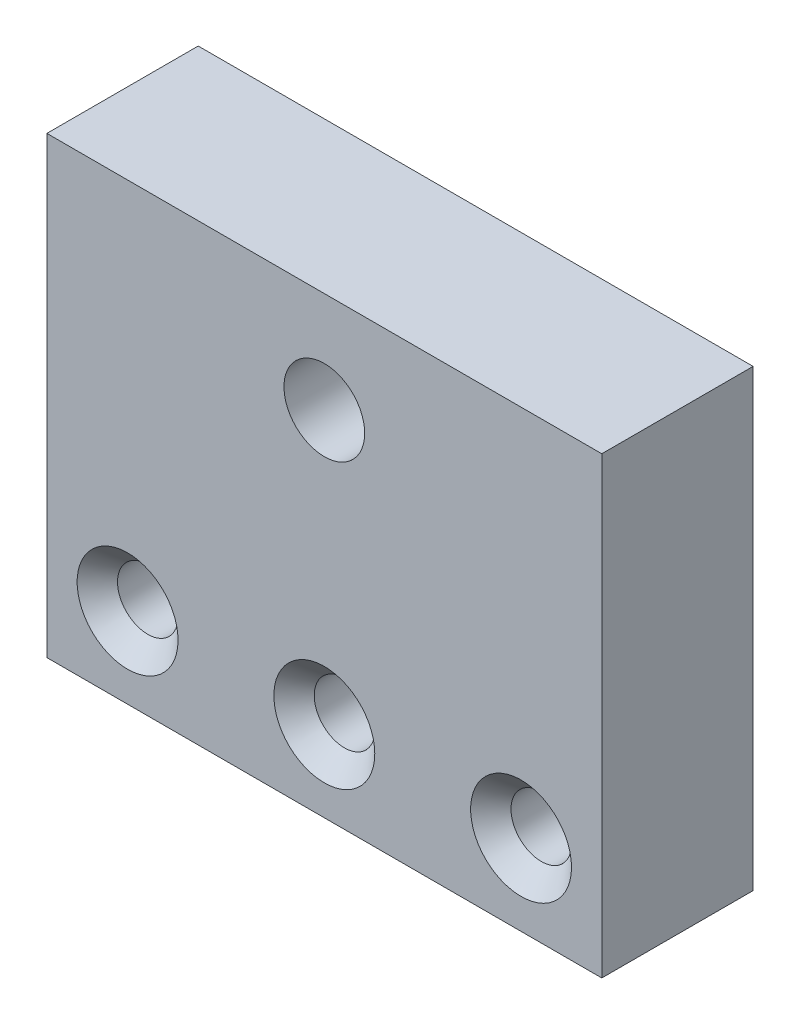
SolidWorks part; units mm, degrees
material "Plain Carbon Steel"
ref_plane "Front Plane" through (0, 0, 0) normal (0, 0, 1) x (1, 0, 0)
ref_plane "Top Plane" through (0, 0, 0) normal (0, 1, 0) x (1, 0, 0)
ref_plane "Right Plane" through (0, 0, 0) normal (1, 0, 0) x (0, 0, -1)
sketch "Sketch1" plane through (0, 0, 0) normal (0, 0, 1) x (1, 0, 0)
  line L1 (0, 0) -> (55, 0)
  line L2 (0, 0) -> (0, 45)
  line L3 (0, 45) -> (55, 45)
  line L4 (55, 0) -> (55, 45)
  dimension "D1" = 55
  dimension "D2" = 45
extrude "Boss-Extrude1" add sketch "Sketch1" along normal mid plane 15
hole_wizard "Ø6.0mm Dowel Hole1" positions "3DSketch1" profile "Sketch2" hole size "Ø6.0" standard "ANSI Metric" end condition through all
sketch3d "3DSketch1"
  line L0 (0, 0, 7.5) -> (55, 0, 7.5) construction
  point P0 (8, 8, 7.5)
  point P2 (27.5, 8, 7.5)
  point P4 (47, 8, 7.5)
  dimension "D1" = 8
sketch "Sketch2" plane through (8, 8, 7.5) normal (1, 0, 0) x (0, -1, 0)
  line L0 (0, 0) -> (0, 15)
  line L1 (0, 15) -> (3, 15)
  line L2 (3, 15) -> (3, 2)
  line L3 (3, 2) -> (5, 0)
  line L5 (5, 0) -> (0, 0)
  line L6 (-3, 2) -> (-5, 0) construction
  line L11 (0, -6.35) -> (0, 107.95) construction
  dimension "Thru Hole Dia." = 6
  dimension "Thru Hole Depth" = 15
  dimension "Near C'Sink Dia." = 10
  dimension "Near C'Sink Angle" = 90
hole_wizard "Ø8.0mm Dowel Hole1" positions "3DSketch4" profile "Sketch5" hole size "Ø8.0" standard "ANSI Metric" end condition through all
sketch3d "3DSketch4"
  point P0 (27.5, 35, 7.5)
sketch "Sketch5" plane through (27.5, 35, 7.5) normal (1, 0, 0) x (0, -1, 0)
  line L0 (0, 0) -> (0, 15)
  line L1 (0, 15) -> (4, 15)
  line L2 (4, 15) -> (4, 0)
  line L5 (4, 0) -> (0, 0)
  line L11 (0, -6.35) -> (0, 107.95) construction
  dimension "Thru Hole Dia." = 8
  dimension "Thru Hole Depth" = 15
